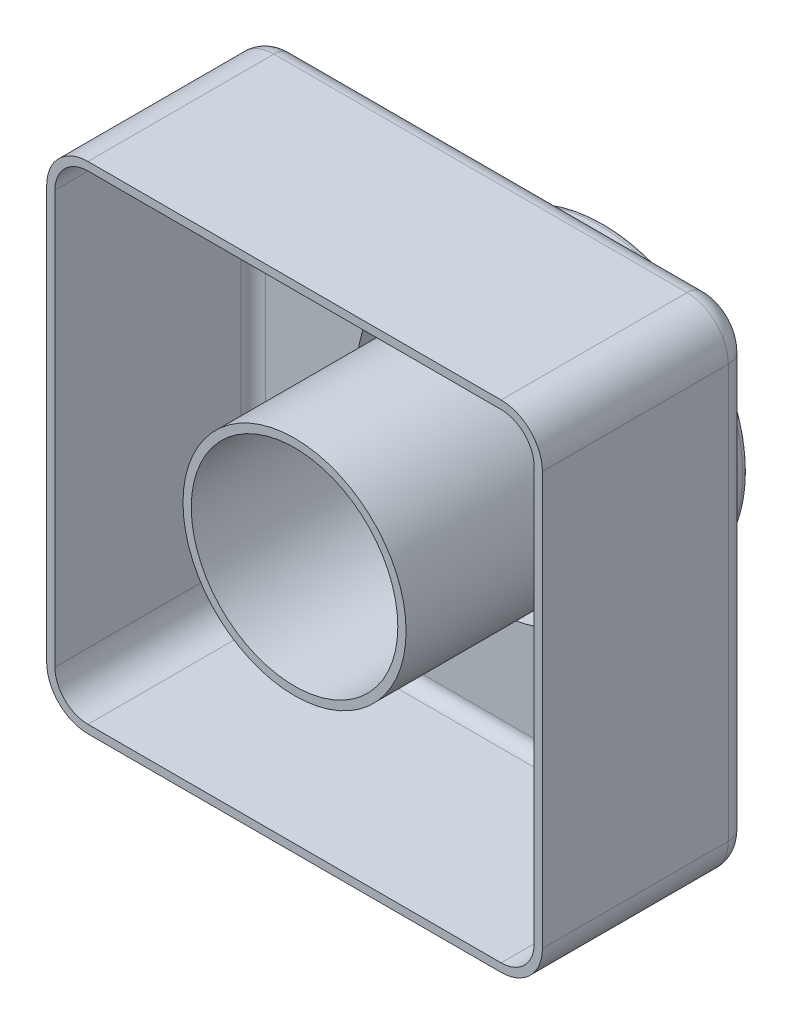
SolidWorks part; units mm, degrees
ref_plane "Front Plane" through (0, 0, 0) normal (0, 0, 1) x (1, 0, 0)
ref_plane "Top Plane" through (0, 0, 0) normal (0, 1, 0) x (1, 0, 0)
ref_plane "Right Plane" through (0, 0, 0) normal (1, 0, 0) x (0, 0, -1)
sketch "Sketch2" plane through (0, 0, 0) normal (0, 0, 1) x (1, 0, 0)
  line L0 (0, 60) -> (0, -60) construction
  line L1 (-60, 60) -> (60, 60)
  line L2 (-60, 60) -> (-60, -60)
  line L3 (-60, -60) -> (60, -60)
  line L4 (60, 60) -> (60, -60)
  line L5 (60, 0) -> (-60, 0) construction
  point P8 (0, 0)
  dimension "D1" = 120
  dimension "D2" = 120
extrude "Boss-Extrude1" add sketch "Sketch2" along normal blind 50
sketch "Sketch3" plane through (0, 0, 0) normal (0, 0, -1) x (-1, 0, 0)
  circle A0 centre (0, 0) radius 35
  dimension "D1" = 70
extrude "Boss-Extrude2" add sketch "Sketch3" along normal blind 25
sketch "Sketch4" plane through (0, 0, -25) normal (0, 0, -1) x (-1, 0, 0)
  circle A0 centre (0, 0) radius 25
  dimension "D1" = 50
extrude "Cut-Extrude1" cut sketch "Sketch4" against normal through all
fillet "Fillet2" radius 1.5 2 edges at (-35, 0, -25) (-25, 0, -25)
fillet "Fillet7" radius 10 4 edges at (-60, -60, 25) (60, -60, 25) (-60, 60, 25) (60, 60, 25)
fillet "Fillet8" radius 5 8 edges at (57.0711, 57.0711, 0) (57.0711, -57.0711, 0) (-57.0711, -57.0711, 0) (-57.0711, 57.0711, 0) (0, -60, 0) (-60, 0, 0) (60, 0, 0) (0, 60, 0)
shell "Shell1" thickness 2
